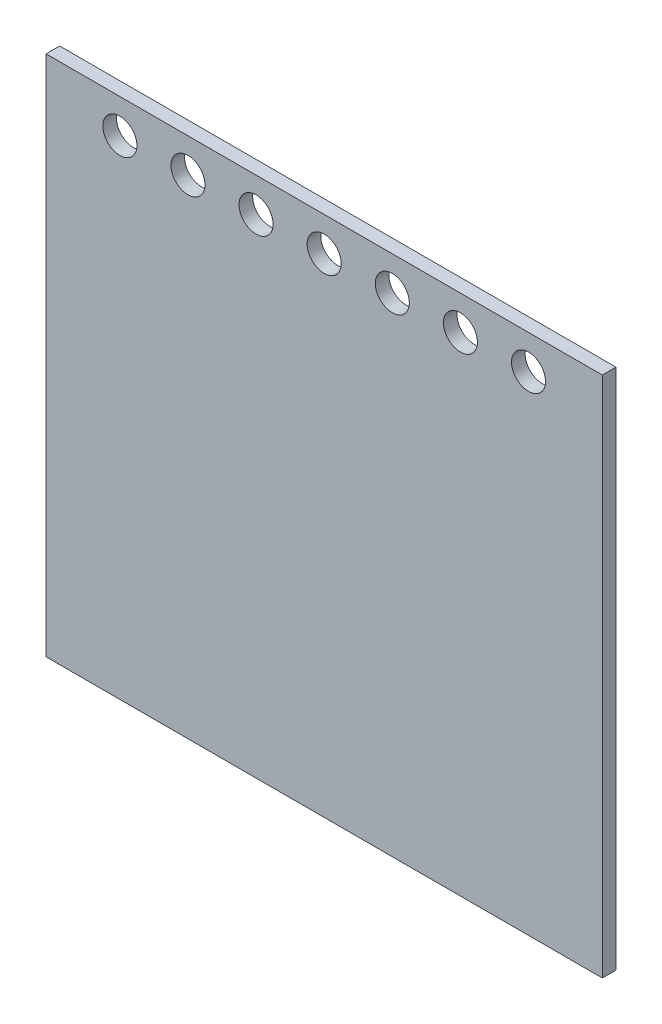
SolidWorks part; units mm, degrees
ref_plane "Front Plane" through (0, 0, 0) normal (0, 0, 1) x (1, 0, 0)
ref_plane "Top Plane" through (0, 0, 0) normal (0, 1, 0) x (1, 0, 0)
ref_plane "Right Plane" through (0, 0, 0) normal (1, 0, 0) x (0, 0, -1)
sketch "Sketch1" plane through (0, 0, 0) normal (0, 0, 1) x (1, 0, 0)
  line L1 (-367.5, -345) -> (367.5, -345)
  line L2 (-367.5, -345) -> (-367.5, 345)
  line L3 (-367.5, 345) -> (367.5, 345)
  line L4 (367.5, -345) -> (367.5, 345)
  line L5 (-367.5, -345) -> (367.5, 345) construction
  line L6 (-367.5, 345) -> (367.5, -345) construction
  circle A0 centre (0, 300) radius 22.5
  circle A1 centre (90, 300) radius 22.5
  circle A2 centre (180, 300) radius 22.5
  circle A3 centre (270, 300) radius 22.5
  circle A4 centre (-90, 300) radius 22.5
  circle A5 centre (-180, 300) radius 22.5
  circle A6 centre (-270, 300) radius 22.5
  point P0 (0, 0)
  dimension "D3" = 45
  dimension "D6" = 45
  dimension "D7" = 0
  dimension "D1" = 735
  dimension "D2" = 690
  dimension "D4" = 4
  dimension "D5" = 4
extrude "Boss-Extrude1" add sketch "Sketch1" along normal blind 18
